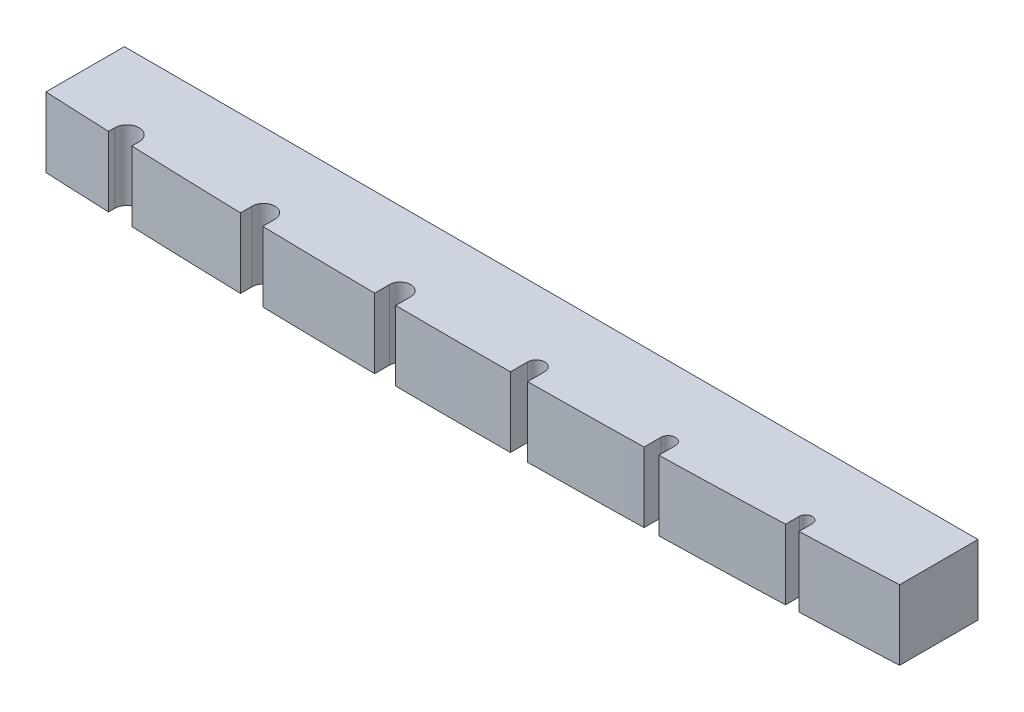
SolidWorks part; units mm, degrees
ref_plane "Front Plane" through (0, 0, 0) normal (0, 0, 1) x (1, 0, 0)
ref_plane "Top Plane" through (0, 0, 0) normal (0, 1, 0) x (1, 0, 0)
ref_plane "Right Plane" through (0, 0, 0) normal (1, 0, 0) x (0, 0, -1)
sketch "Sketch1" plane through (0, 0, 0) normal (0, 1, 0) x (1, 0, 0)
  line L1 (0, 0) -> (41.91, 0)
  line L2 (0, 0) -> (0, 4.3561)
  line L3 (0, 4.3561) -> (41.91, 4.3561)
  line L4 (41.91, 0) -> (41.91, 4.3561)
  dimension "D1" = 4.3561
  dimension "D2" = 41.91
extrude "Boss-Extrude1" add sketch "Sketch1" along normal blind 3.429
sketch "Sketch3" plane through (0, 3.429, 0) normal (0, 1, 0) x (1, 0, 0)
  line L0 (0, 0) -> (41.91, 0) construction
  line L1 (3.2131, 0) -> (3.2131, 0.6734)
  line L3 (4.4069, 0) -> (4.4069, 0.6728)
  line L4 (3.2131, 0) -> (4.4069, 0)
  line L5 (9.9187, 0) -> (9.9187, 0.7112)
  line L6 (11.0363, 0) -> (11.0363, 0.7112)
  line L7 (9.9187, 0) -> (11.0363, 0)
  line L8 (16.6243, 0) -> (16.6243, 0.7493)
  line L9 (17.6657, 0) -> (17.6657, 0.7493)
  line L10 (16.6243, 0) -> (17.6657, 0)
  line L11 (23.3045, 0) -> (23.3045, 0.8509)
  line L12 (24.1427, 0) -> (24.1427, 0.8509)
  line L13 (23.3045, 0) -> (24.1427, 0)
  line L14 (29.7815, 0) -> (29.7815, 0.9144)
  line L15 (30.4927, 0) -> (30.4927, 0.9144)
  line L16 (29.7815, 0) -> (30.4927, 0)
  line L17 (36.5379, 0) -> (36.5379, 0.9525)
  line L18 (37.1729, 0) -> (37.1729, 0.9525)
  line L19 (36.5379, 0) -> (37.1729, 0)
  arc A0 (3.2131, 0.6734) -> (4.4069, 0.6728) centre (3.81, 0.6731) cw
  arc A1 (9.9187, 0.7112) -> (11.0363, 0.7112) centre (10.4775, 0.7112) cw
  arc A2 (16.6243, 0.7493) -> (17.6657, 0.7493) centre (17.145, 0.7493) cw
  arc A3 (23.3045, 0.8509) -> (24.1427, 0.8509) centre (23.7236, 0.8509) cw
  arc A4 (29.7815, 0.9144) -> (30.4927, 0.9144) centre (30.1371, 0.9144) cw
  arc A5 (36.5379, 0.9525) -> (37.1729, 0.9525) centre (36.8554, 0.9525) cw
  point P11 (10.4775, 1.27)
  point P18 (17.145, 1.27)
  point P20 (3.8103, 1.27)
  point P30 (23.7236, 1.27)
  point P37 (30.1371, 1.27)
  point P44 (36.8554, 1.27)
  dimension "D2" = 1.27
  dimension "D4" = 0.5969
  dimension "D6" = 1.27
  dimension "D20" = 1.27
  dimension "D1" = 1.1938
  dimension "D3" = 3.2131
  dimension "D5" = 0.5972
  dimension "D7" = 1.1176
  dimension "D8" = 5.5118
  dimension "D9" = 5.588
  dimension "D10" = 1.0414
  dimension "D11" = 1.27
  dimension "D12" = 5.6388
  dimension "D13" = 0.8382
  dimension "D14" = 1.27
  dimension "D15" = 5.6388
  dimension "D16" = 0.7112
  dimension "D17" = 1.27
  dimension "D18" = 6.0452
  dimension "D19" = 0.635
extrude "Cut-Extrude1" cut sketch "Sketch3" against normal up to surface (3.429 mm away) up to face at (20.955, 0, -2.178)
sketch "Sketch4" plane through (0, 3.429, 0) normal (0, 1, 0) x (1, 0, 0)
  line L0 (0, 0) -> (0, 0.508) construction
  line L1 (0, 4.3561) -> (0, 0) construction
  line L2 (0, 0.508) -> (41.91, 0.508) construction
  line L3 (41.91, 0) -> (41.91, 4.3561) construction
  line L4 (0, 0.508) -> (0, -0.5386)
  line L5 (0, -0.5386) -> (41.91, -0.5386)
  line L6 (41.91, -0.5386) -> (41.91, 0.508)
  line L7 (41.91, 4.3561) -> (0, 4.3561) construction
  arc A0 (0, 0.508) -> (41.91, 0.508) centre (20.955, 432.4509) ccw
  dimension "D2" = 432.4509
  dimension "D1" = 0.508
  dimension "D3" = 4.8947
extrude "Cut-Extrude2" cut sketch "Sketch4" against normal up to next
